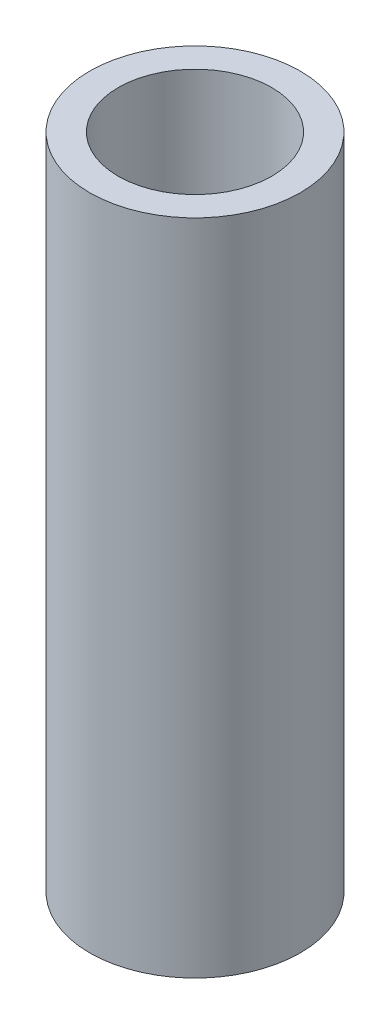
SolidWorks part; units mm, degrees
ref_plane "Front Plane" through (0, 0, 0) normal (0, 0, 1) x (1, 0, 0)
ref_plane "Top Plane" through (0, 0, 0) normal (0, 1, 0) x (1, 0, 0)
ref_plane "Right Plane" through (0, 0, 0) normal (1, 0, 0) x (0, 0, -1)
sketch "Sketch2" plane through (0, 0, 0) normal (0, 1, 0) x (1, 0, 0)
  circle A0 centre (0, 0) radius 2.4
  dimension "D1" = 4.8
extrude "Boss-Extrude1" add sketch "Sketch2" along normal blind 15
sketch "Sketch3" plane through (0, 15, 0) normal (0, 1, 0) x (1, 0, 0)
  circle A0 centre (0, 0) radius 1.75
  dimension "D1" = 3.5
extrude "Cut-Extrude1" cut sketch "Sketch3" against normal blind 15
